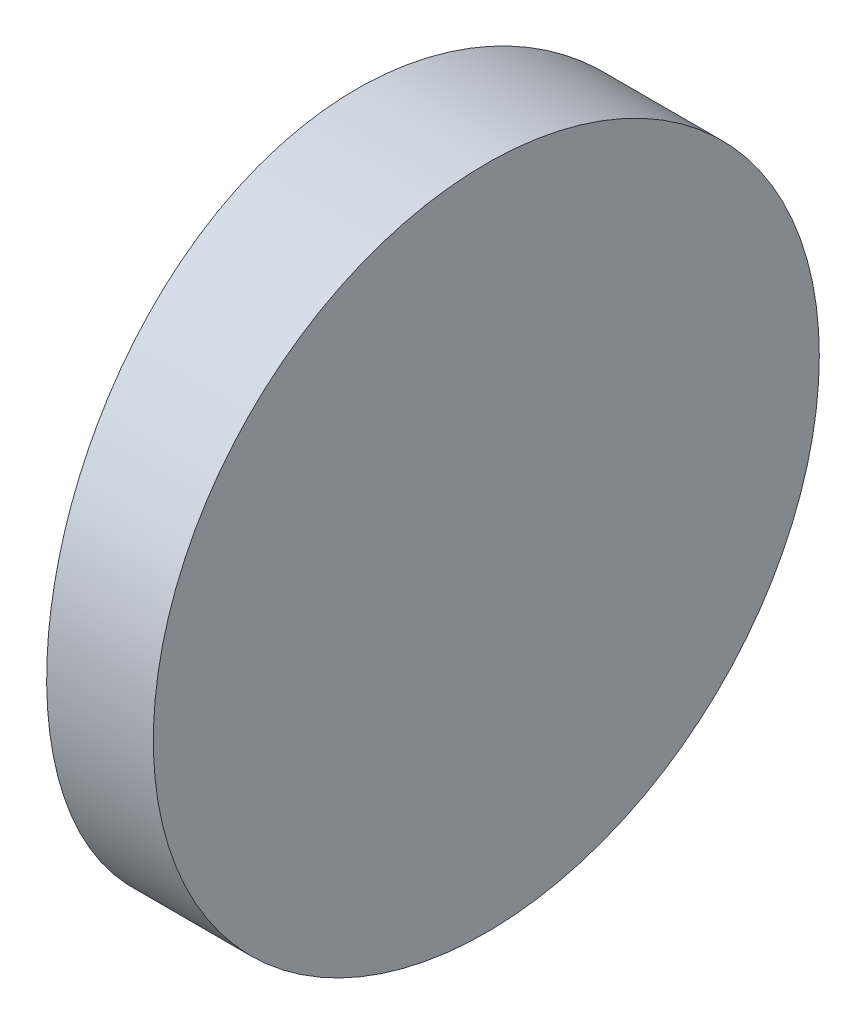
SolidWorks part; units mm, degrees
ref_plane "前视基准面" through (0, 0, 0) normal (0, 0, 1) x (1, 0, 0)
ref_plane "上视基准面" through (0, 0, 0) normal (0, 1, 0) x (1, 0, 0)
ref_plane "右视基准面" through (0, 0, 0) normal (1, 0, 0) x (0, 0, -1)
sketch "草图1" plane through (0, 0, 0) normal (0, 1, 0) x (1, 0, 0)
  line L0 (10.7432, 0) -> (-53.9538, 0) construction
  line L1 (-41.0668, 6.25) -> (-39.0648, 6.25)
  line L2 (-41.0668, -6.25) -> (-39.0648, -6.25)
  line L3 (-39.0648, 6.25) -> (-39.0648, -6.25)
  arc A0 (-41.0668, 6.25) -> (-41.0668, -6.25) centre (4.3552, 0) ccw
  point P2 (-33.6622, 0)
  point P4 (-53.9538, 0)
  point P19 (-41.4948, 0)
  point P20 (-39.0648, 0)
  dimension "D2" = 6.25
  dimension "D3" = 45.85
  dimension "D4" = 2.43
  dimension "D1" = 6.25
extrude "凸台-拉伸1" add sketch "草图1" along normal blind 12.5 contours A0 L2 L3 L1
sketch "草图2" plane through (-39.0648, 0, 0) normal (1, 0, 0) x (0, 0, -1)
  line L0 (6.25, 0) -> (-6.25, 0) construction
  line L7 (-6.25, 0) -> (6.25, 0)
  line L8 (6.25, 0) -> (6.25, 12.5)
  line L9 (6.25, 12.5) -> (-6.25, 12.5)
  line L10 (-6.25, 12.5) -> (-6.25, 0)
  line L11 (-6.25, 0) -> (6.25, 0)
  line L12 (6.25, 0) -> (6.25, 12.5)
  line L13 (6.25, 12.5) -> (-6.25, 12.5)
  line L14 (-6.25, 12.5) -> (-6.25, 0)
  circle A0 centre (0, 6.25) radius 6.25
  line M1 (-6.25, 0) -> (6.25, 0)
  line M2 (6.25, 0) -> (6.25, 12.5)
  line M3 (6.25, 12.5) -> (-6.25, 12.5)
  line M4 (-6.25, 12.5) -> (-6.25, 0)
  dimension "D1" = 12.5
  dimension "D2" = 6.25
  dimension "D3" = 0
extrude "切除-拉伸8" cut sketch "草图2" against normal blind 12.7 contours A0 L13 M4 | A0 L12 M3 | A0 L11 M2 | A0 L14 M1
